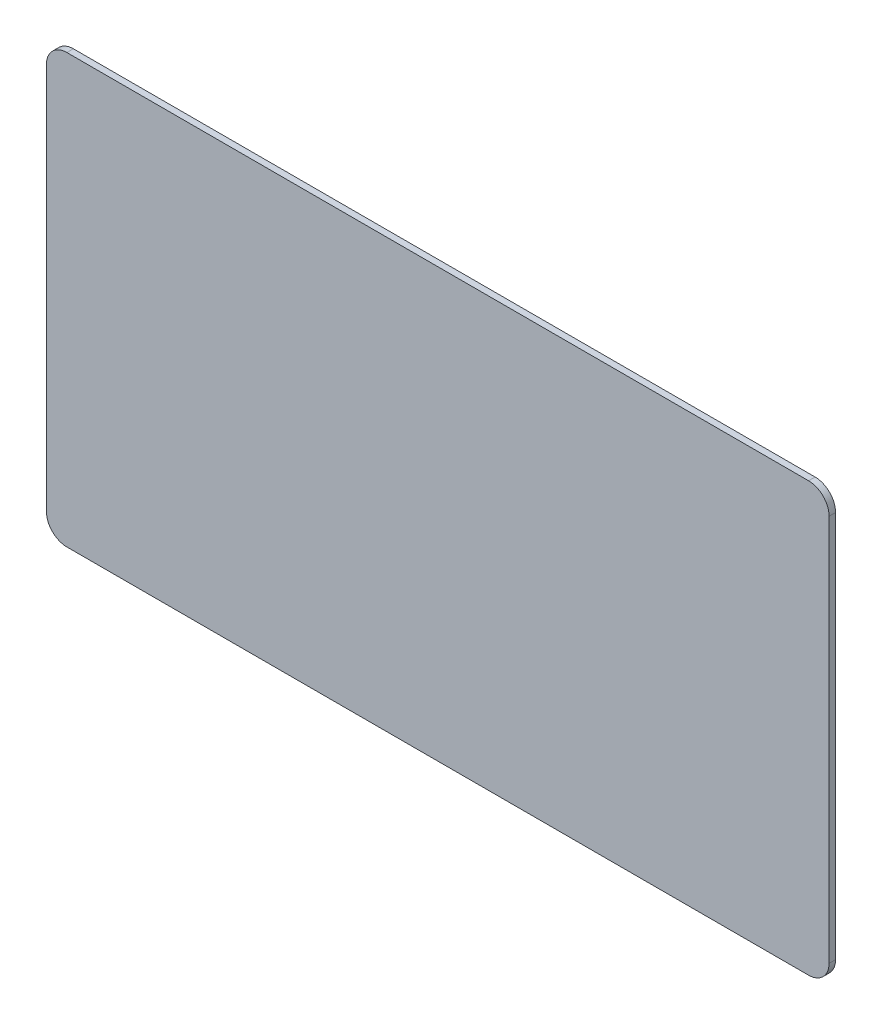
SolidWorks part; units mm, degrees
ref_plane "Front Plane" through (0, 0, 0) normal (0, 0, 1) x (1, 0, 0)
ref_plane "Top Plane" through (0, 0, 0) normal (0, 1, 0) x (1, 0, 0)
ref_plane "Right Plane" through (0, 0, 0) normal (1, 0, 0) x (0, 0, -1)
sketch "Sketch1" plane through (0, 0, 0) normal (0, 0, 1) x (1, 0, 0)
  line L1 (10, 0) -> (372, 0)
  line L2 (0, -10) -> (0, -199)
  line L3 (10, -209) -> (372, -209)
  line L4 (382, -10) -> (382, -199)
  arc A0 (372, 0) -> (382, -10) centre (372, -10) cw
  arc A1 (372, -209) -> (382, -199) centre (372, -199) ccw
  arc A2 (0, -199) -> (10, -209) centre (10, -199) ccw
  arc A3 (10, 0) -> (0, -10) centre (10, -10) ccw
  point P13 (0, 0)
  dimension "D1" = 10
  dimension "D2" = 209
  dimension "D3" = 362
extrude "Boss-Extrude1" add sketch "Sketch1" along normal blind 3.175
